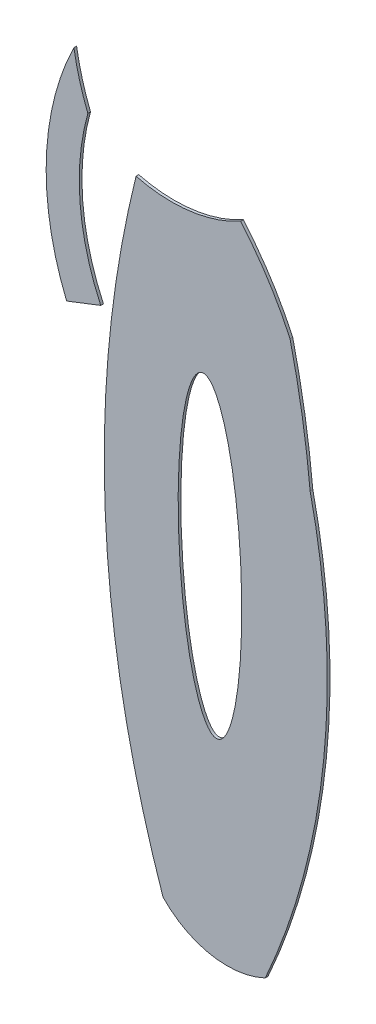
SolidWorks part; units mm, degrees
ref_plane "Alzado" through (0, 0, 0) normal (0, 0, 1) x (1, 0, 0)
ref_plane "Planta" through (0, 0, 0) normal (0, 1, 0) x (1, 0, 0)
ref_plane "Vista lateral" through (0, 0, 0) normal (1, 0, 0) x (0, 0, -1)
sketch "Model" plane through (0, 0, 0) normal (0, 0, 1) x (1, 0, 0)
  line L0 (8.1645, -25.9121) -> (9.4345, -25.4186)
  arc A0 (8.4356, -17.6111) -> (8.1645, -25.9121) centre (17.529, -22.063) ccw
  arc A1 (15.554, -44.0251) -> (17.2224, -27.5025) centre (-8.4052, -33.2602) ccw
  arc A2 (11.7528, -43.3237) -> (15.554, -44.0251) centre (14.1393, -41.0411) ccw
  arc A3 (10.7485, -20.5994) -> (11.7528, -43.3237) centre (49.622, -30.2657) ccw
  arc A4 (8.954, -19.4723) -> (9.4345, -25.4186) centre (17.2599, -21.7937) ccw
  arc A5 (8.4356, -17.6111) -> (8.954, -19.4723) centre (17.2836, -16.1495) ccw
  arc A6 (10.7485, -20.5994) -> (14.6357, -20.106) centre (12.0677, -15.4333) ccw
  arc A7 (16.4752, -22.97) -> (14.6357, -20.106) centre (5.3307, -28.1052) ccw
  arc A8 (17.2224, -27.5025) -> (16.4752, -22.97) centre (-15.6544, -30.5948) ccw
  ellipse E0 centre (13.4972, -31.4546) end of major axis (13.2472, -25.6925) minor radius 1.1575
extrude "Saliente-Extruir1" add sketch "Model" along normal blind 0.1
